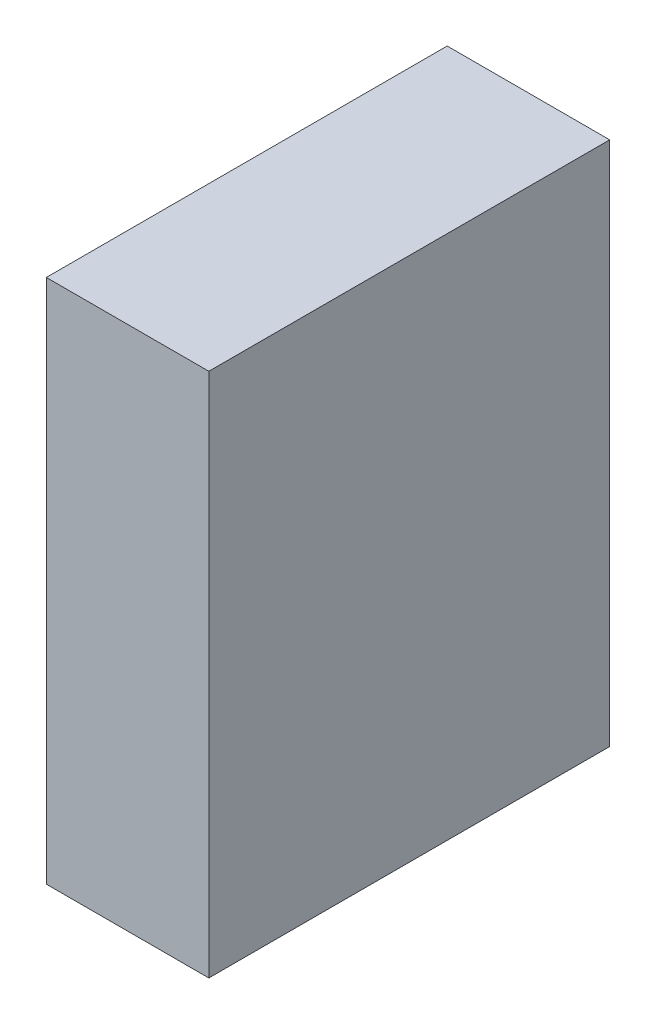
SolidWorks part; units mm, degrees
ref_plane "Plan de face" through (0, 0, 0) normal (0, 0, 1) x (1, 0, 0)
ref_plane "Plan de dessus" through (0, 0, 0) normal (0, 1, 0) x (1, 0, 0)
ref_plane "Plan de droite" through (0, 0, 0) normal (1, 0, 0) x (0, 0, -1)
sketch "Esquisse1" plane through (0, 0, 0) normal (1, 0, 0) x (0, 0, -1)
  line L1 (-37, -48.5) -> (37, -48.5)
  line L2 (-37, -48.5) -> (-37, 48.5)
  line L3 (-37, 48.5) -> (37, 48.5)
  line L4 (37, -48.5) -> (37, 48.5)
  line L5 (-37, -48.5) -> (37, 48.5) construction
  line L6 (-37, 48.5) -> (37, -48.5) construction
  point P0 (0, 0)
  dimension "D1" = 74
extrude "Boss.-Extru.1" add sketch "Esquisse1" along normal blind 30
